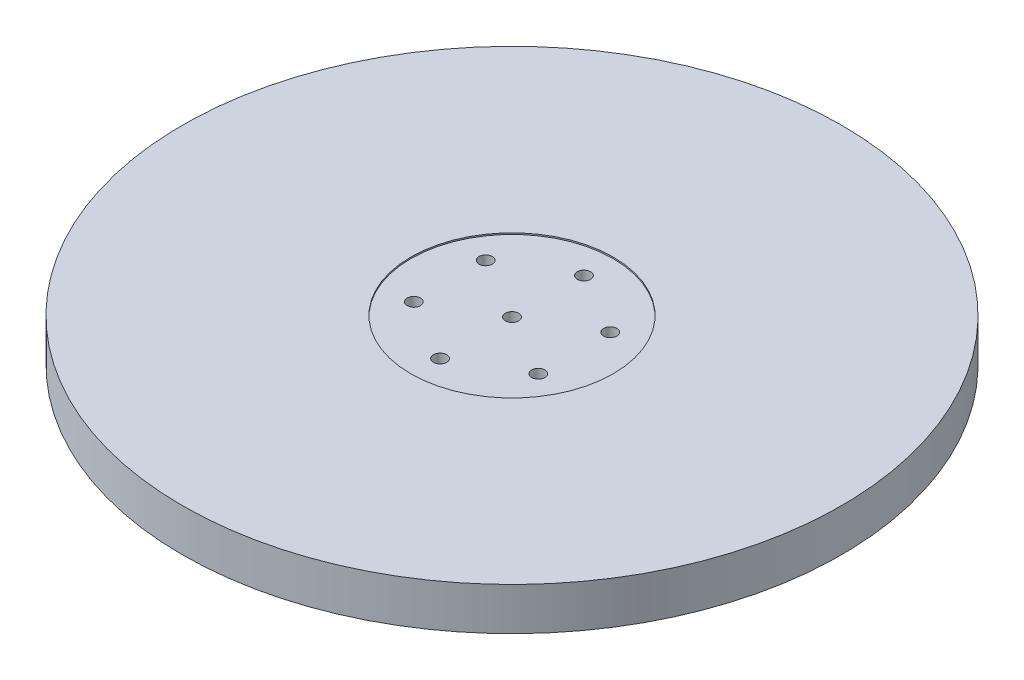
SolidWorks part; units mm, degrees
ref_plane "Alzado" through (0, 0, 0) normal (0, 0, 1) x (1, 0, 0)
ref_plane "Planta" through (0, 0, 0) normal (0, 1, 0) x (1, 0, 0)
ref_plane "Vista lateral" through (0, 0, 0) normal (1, 0, 0) x (0, 0, -1)
sketch "Croquis1" plane through (0, 0, 0) normal (0, 1, 0) x (1, 0, 0)
  circle A0 centre (0, 0) radius 61.8856
  dimension "D1" = 123.7713
extrude "Saliente-Extruir1" add sketch "Croquis1" along normal blind 8
sketch "Croquis2" plane through (0, 8, 0) normal (0, 1, 0) x (1, 0, 0)
  circle A0 centre (0, 0) radius 20
  dimension "D1" = 40
extrude "Cortar-Extruir1" cut sketch "Croquis2" against normal blind 8
sketch "Croquis3" plane through (0, 8, 0) normal (0, 1, 0) x (1, 0, 0)
  circle A0 centre (0, 0) radius 20
extrude "Saliente-Extruir2" add sketch "Croquis3" against normal blind 4
sketch "Croquis4" plane through (0, 4, 0) normal (0, -1, 0) x (-1, 0, 0)
  circle A0 centre (0, 0) radius 19
  dimension "D1" = 38
extrude "Saliente-Extruir3" add sketch "Croquis4" against normal blind 8.1661
sketch "Croquis5" plane through (0, 12.1661, 0) normal (0, 1, 0) x (1, 0, 0)
  line L0 (0, 0) -> (0, 19) construction
  line L1 (0, 0) -> (0, -19) construction
  circle A0 centre (0, 0) radius 19 construction
  circle A1 centre (0, 13.5) radius 1.25
  circle A2 centre (0, -13.5) radius 1.25
  circle A3 centre (11.6913, 6.75) radius 1.25
  circle A4 centre (11.6913, -6.75) radius 1.25
  circle A5 centre (0, -13.5) radius 1.25
  circle A6 centre (-11.6913, -6.75) radius 1.25
  circle A7 centre (-11.6913, 6.75) radius 1.25
  point P23 (0, 0)
  dimension "D1" = 2.5
  dimension "D2" = 2.5
  dimension "D3" = 27
  dimension "D4" = 13.5
  dimension "D5" = 6
extrude "Cortar-Extruir2" cut sketch "Croquis5" against normal blind 8.1661 contours A3 | A1 | A7 | A6 | A2 | A4
sketch "Croquis6" plane through (0, 12.1661, 0) normal (0, 1, 0) x (1, 0, 0)
  circle A0 centre (0, 0) radius 1.25
  dimension "D1" = 2.5
extrude "Cortar-Extruir3" cut sketch "Croquis6" against normal blind 8.1661
sketch "Croquis7" plane through (0, 12.1661, 0) normal (0, 1, 0) x (1, 0, 0)
  circle A0 centre (0, 0) radius 19
extrude "Cortar-Extruir4" cut sketch "Croquis7" against normal blind 4.43
